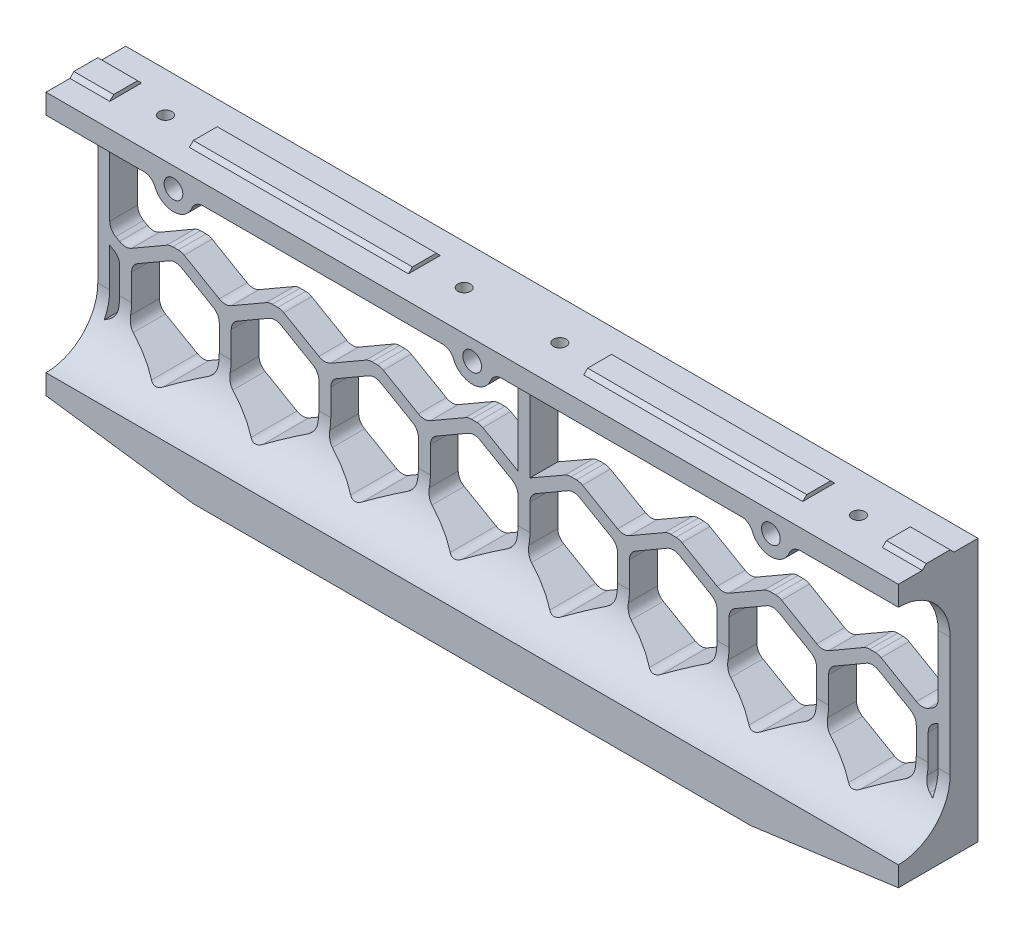
SolidWorks part; units mm, degrees
ref_plane "Front Plane" through (0, 0, 0) normal (0, 0, 1) x (1, 0, 0)
ref_plane "Top Plane" through (0, 0, 0) normal (0, 1, 0) x (1, 0, 0)
ref_plane "Right Plane" through (0, 0, 0) normal (1, 0, 0) x (0, 0, -1)
sketch "Sketch1" plane through (0, 0, 0) normal (1, 0, 0) x (0, 0, -1)
  line L0 (20, 0) -> (14, 0)
  line L1 (0, 0) -> (0, -66)
  line L2 (0, -66) -> (5, -66)
  line L3 (5, -66) -> (11, -62)
  line L4 (11, -62) -> (20, -62)
  line L5 (20, -62) -> (20, 0)
  line L6 (6, 0) -> (7, 1)
  line L7 (7, 1) -> (13, 1)
  line L8 (13, 1) -> (14, 0)
  line L9 (6, 0) -> (0, 0)
  dimension "D1" = 20
  dimension "D2" = 62
  dimension "D3" = 66
  dimension "D4" = 9
  dimension "D5" = 5
  dimension "D6" = 6
  dimension "D7" = 1
  dimension "D8" = 6
  dimension "D9" = 135
  dimension "D10" = 135
  dimension "D11" = 6
extrude "Boss-Extrude1" add sketch "Sketch1" along normal blind 107
sketch "Sketch8" plane through (0, -62, 0) normal (0, -1, 0) x (1, 0, 0)
  line L1 (0, -20) -> (70, -20)
  line L2 (0, -20) -> (0, 0)
  line L3 (0, 0) -> (70, 0)
  line L4 (70, -20) -> (70, 0)
  line L5 (0, -20) -> (70, 0) construction
  line L6 (0, 0) -> (70, -20) construction
  point P4 (35, -10)
  dimension "D1" = 70
extrude "Boss-Extrude2" add sketch "Sketch8" along normal blind 9
sketch "Sketch2" plane through (0, 1, 0) normal (0, 1, 0) x (1, 0, 0)
  line L0 (107, 14) -> (0, 14) construction
  line L1 (77, 14) -> (97, 14)
  line L2 (77, 14) -> (77, 6)
  line L3 (77, 6) -> (97, 6)
  line L4 (97, 14) -> (97, 6)
  line L5 (77, 14) -> (97, 6) construction
  line L6 (77, 6) -> (97, 14) construction
  line L7 (107, 6) -> (0, 6) construction
  line L8 (107, 13) -> (107, 7) construction
  line L14 (0, 14) -> (22, 14)
  line L15 (0, 14) -> (0, 6)
  line L16 (0, 6) -> (22, 6)
  line L17 (22, 14) -> (22, 6)
  line L18 (0, 14) -> (22, 6) construction
  line L19 (0, 6) -> (22, 14) construction
  point P4 (87, 10)
  point P17 (11, 10)
  dimension "D1" = 20
  dimension "D2" = 10
  dimension "D3" = 22
extrude "RailBump" cut sketch "Sketch2" against normal up to surface (1 mm away) up to face at (53.5, 0, -17)
sketch "Sketch3" plane through (0, 0, 0) normal (0, 1, 0) x (1, 0, 0)
  line L0 (107, 0) -> (0, 0) construction
  line L1 (22, 6) -> (22, 14) construction
  line L4 (97, 7) -> (97, 13) construction
  circle A0 centre (87, 10) radius 1.6
  circle A1 centre (12, 10) radius 1.6
  dimension "D2" = 10
  dimension "D3" = 3.2
  dimension "D4" = 10
  dimension "D5" = 10
  dimension "D1" = 10
extrude "RailMountHole" cut sketch "Sketch3" against normal blind 5
sketch "Sketch6" plane through (0, 0, 0) normal (0, 1, 0) x (1, 0, 0)
  circle A0 centre (87, 10) radius 3
  circle A1 centre (12, 10) radius 3
  dimension "D1" = 6
extrude "Mounting hole clearance" cut sketch "Sketch6" against normal blind 10 from offset 4 offset against normal yes
sketch "Sketch4" plane through (0, 0, -20) normal (0, 0, -1) x (-1, 0, 0)
  line L0 (0, 19.0302) -> (0, -62.788) construction
  line L41 (-61, -30.6998) -> (-50, -37.0506)
  line L42 (-50, -37.0506) -> (-39, -30.6998)
  line L47 (-36, -30.6998) -> (-25, -37.0506)
  line L48 (-25, -37.0506) -> (-14, -30.6998)
  line L53 (-11, -30.6998) -> (-1.5, -36.1271)
  line L55 (-107, -62) -> (-107, 0) construction
  line L56 (-104, -5) -> (-1.5, -5)
  line L57 (4.3823, -24.3489) -> (-107, -24.3489) construction
  line L61 (-39, -30.6998) -> (-36, -30.6998)
  line L62 (-107, 0) -> (0, 0) construction
  line L64 (-37.5, -58.7013) -> (-26.5, -52.3504)
  line L65 (-26.5, -52.3504) -> (-26.5, -39.6487)
  line L66 (-26.5, -39.6487) -> (-37.5, -33.2979)
  line L67 (-37.5, -33.2979) -> (-48.5, -39.6487)
  line L68 (-48.5, -39.6487) -> (-48.5, -52.3504)
  line L69 (-48.5, -52.3504) -> (-37.5, -58.7013)
  line L70 (-12.5, -58.7013) -> (-1.5, -52.3504)
  line L71 (-1.5, -52.3504) -> (-1.5, -39.6487)
  line L72 (-1.5, -39.6487) -> (-12.5, -33.2979)
  line L73 (-12.5, -33.2979) -> (-23.5, -39.6487)
  line L74 (-23.5, -39.6487) -> (-23.5, -52.3504)
  line L75 (-23.5, -52.3504) -> (-12.5, -58.7013)
  line L107 (-14, -30.6998) -> (-11, -30.6998)
  line L108 (-64, -30.6998) -> (-61, -30.6998)
  line L110 (-89, -30.7162) -> (-86, -30.6998)
  line L111 (-1.5, -5) -> (-1.5, -36.1271)
  line L118 (-86, -30.6998) -> (-75, -37.0506)
  line L119 (-75, -37.0506) -> (-64, -30.6998)
  line L124 (-104, -34.7904) -> (-100.0284, -37.0834)
  line L125 (-100.0284, -37.0834) -> (-89, -30.7162)
  line L126 (-61, -17.6718) -> (-61, -24.0227) [skipped]
  line L127 (-104, -5) -> (-104, -34.7904)
  line L131 (-76.5, -52.3504) -> (-76.5, -39.6487)
  line L132 (-76.5, -39.6487) -> (-87.5, -33.2979)
  line L133 (-87.5, -33.2979) -> (-98.5, -39.6487)
  line L134 (-98.5, -39.6487) -> (-98.5, -52.3504)
  line L135 (-98.5, -52.3504) -> (-87.5, -58.7013)
  line L136 (-87.5, -58.7013) -> (-76.5, -52.3504)
  line L137 (-51.5, -52.3504) -> (-51.5, -39.6487)
  line L138 (-51.5, -39.6487) -> (-62.5, -33.2979)
  line L139 (-62.5, -33.2979) -> (-73.5, -39.6487)
  line L140 (-73.5, -39.6487) -> (-73.5, -52.3504)
  line L141 (-73.5, -52.3504) -> (-62.5, -58.7013)
  line L142 (-62.5, -58.7013) -> (-51.5, -52.3504)
  line L158 (-101.5, -39.6979) -> (-104, -38.2545)
  line L162 (-104, -53.8184) -> (-101.5, -52.375)
  line L163 (-101.5, -52.375) -> (-101.5, -39.6979)
  line L174 (-111.0568, -24.3489) -> (-111.0568, -30.6998) [skipped]
  line L175 (-104, -38.2545) -> (-104, -53.8184)
  line L176 (-118.5604, -36.8705) -> (-124.0604, -40.046) [skipped]
  line L177 (-123.4999, -52.3505) -> (-117.9999, -55.5259) [skipped]
  line L178 (-123.4574, -39.6489) -> (-123.4574, -45.9997) [skipped]
  line L185 (0, -71) -> (0, 0) construction
  line L196 (-14, -30.6998) -> (-14, -17.9981) [skipped]
  line L197 (-14, -17.9981) -> (-25, -11.6472) [skipped]
  line L198 (-25, -11.6472) -> (-36, -17.9981) [skipped]
  line L199 (-36, -17.9981) -> (-36, -30.6998) [skipped]
  line L200 (-39, -30.6998) -> (-39, -17.9981) [skipped]
  line L201 (-39, -17.9981) -> (-50, -11.6472) [skipped]
  line L202 (-50, -11.6472) -> (-61, -17.9981) [skipped]
  line L203 (-89, -17.9817) -> (-100.0284, -11.6145) [skipped]
  line L204 (-100.0284, -11.6145) -> (-104, -13.9075) [skipped]
  line L205 (-75, -11.6472) -> (-86, -17.9981) [skipped]
  line L206 (-86, -17.9981) -> (-86, -30.6998) [skipped]
  line L207 (-89, -30.7162) -> (-89, -17.9817) [skipped]
  line L208 (-64, -17.9981) -> (-75, -11.6472) [skipped]
  line L209 (-64, -30.6998) -> (-64, -17.9981) [skipped]
  circle A4 centre (-87.5, -45.9996) radius 11 construction
  circle A5 centre (-62.5, -45.9996) radius 11 construction
  circle A9 centre (-37.5, -45.9996) radius 11 construction
  circle A10 centre (-12.5, -45.9996) radius 11 construction
  circle A14 centre (-112.4787, -46.0364) radius 10.9787 construction
  point P0 (-1.5, -36.1271)
  dimension "D5" = 3
  dimension "D7" = 3
  dimension "D8" = 22
  dimension "D9" = 5
  dimension "D15" = 22
  dimension "D17" = 3
  dimension "D18" = 3
  dimension "D19" = 12.7017
  dimension "D20" = 22
  dimension "D21" = 3
  dimension "D28" = 3
  dimension "D29" = 3
  dimension "D30" = 22
  dimension "D37" = 3
  dimension "D40" = 3
  dimension "D41" = 120
  dimension "D44" = 12.6771
  dimension "D48" = 3
  dimension "D49" = 3
extrude "HoneyPatternCutouts" cut sketch "Sketch4" against normal through all
sketch "Sketch5" plane through (107, 0, 0) normal (1, 0, 0) x (0, 0, -1)
  line L0 (0, 0) -> (0, -66) construction
  line L1 (0, -66) -> (5, -66) construction
  line L2 (6, 0) -> (0, 0) construction
  line L3 (13, -18) -> (13, -48)
  line L4 (0, -5) -> (0, -61)
  arc A0 (0, -61) -> (13, -48) centre (0, -48) ccw
  arc A1 (13, -18) -> (0, -5) centre (0, -18) ccw
  dimension "D1" = 26
  dimension "D3" = 26
  dimension "D7" = 13
  dimension "D8" = 13
  dimension "D2" = 18
  dimension "D4" = 18
  dimension "D5" = 30
  dimension "D6" = 5
extrude "Front CarveOut" cut sketch "Sketch5" against normal through all
fillet "Fillet3" radius 3 40 edges at (104, -5, -10) (104, -34.7904, -16.5) (101.5, -52.375, -16.1209) (101.5, -39.6979, -16.5) (98.5, -39.6487, -16.5) (98.5, -52.3504, -16.1252) (100.0284, -37.0834, -16.5) (89, -30.7162, -16.5) (86, -30.6998, -16.5) (87.5, -33.2979, -16.5) (76.5, -39.6487, -16.5) (87.5, -58.7013, -13.6906) (76.5, -52.3504, -16.1252) (62.5, -58.7013, -13.6906) (73.5, -52.3504, -16.1252) (73.5, -39.6487, -16.5) (62.5, -33.2979, -16.5) (75, -37.0506, -16.5) (61, -30.6998, -16.5) (64, -30.6998, -16.5) (51.5, -39.6487, -16.5) (51.5, -52.3504, -16.1252) (48.5, -39.6487, -16.5) (37.5, -33.2979, -16.5) (26.5, -39.6487, -16.5) (26.5, -52.3504, -16.1252) (37.5, -58.7013, -13.6906) (48.5, -52.3504, -16.1252) (50, -37.0506, -16.5) (39, -30.6998, -16.5) (36, -30.6998, -16.5) (25, -37.0506, -16.5) (14, -30.6998, -16.5) (11, -30.6998, -16.5) (1.5, -52.3504, -16.1252) (12.5, -58.7013, -13.6906) (23.5, -52.3504, -16.1252) (23.5, -39.6487, -16.5) (12.5, -33.2979, -16.5) (1.5, -39.6487, -16.5)
mirror "Mirror1" about plane through (0, 0, 0) normal (1, 0, 0) of "Fillet3", "Boss-Extrude2", "Front CarveOut", "RailMountHole", "RailBump", "Boss-Extrude1", "HoneyPatternCutouts", "Mounting hole clearance"
sketch "Sketch22" plane through (0, 0, 0) normal (0, 0, -1) x (-1, 0, 0)
  line L0 (1.5, -5) -> (101, -5) construction
  line L1 (80, -5) -> (70, -5)
  line L3 (-1.5, -5) -> (-101, -5) construction
  line L4 (5, -5) -> (-5, -5)
  line L6 (-80, -5) -> (-70, -5)
  arc A2 (-80, -5) -> (-70, -5) centre (-75, -5) ccw
  arc A3 (-5, -5) -> (5, -5) centre (0, -5) ccw
  arc A4 (70, -5) -> (80, -5) centre (75, -5) ccw
  dimension "D1" = 10
  dimension "D3" = 75
  dimension "D2" = 75
extrude "Boss-Extrude14" add sketch "Sketch22" along normal up to surface (20 mm away) up to face at (-87.5, -45.9996, -20)
sketch "Sketch23" plane through (0, 0, 0) normal (0, 0, -1) x (-1, 0, 0)
  line L2 (0, 0) -> (0, -5) construction
  line L3 (0, -5) -> (-5, -5) construction
  line L4 (-5, -5) -> (-75, -5) construction
  circle A0 centre (-75, -5) radius 2.35
  circle A1 centre (0, -5) radius 2.35
  circle A2 centre (75, -5) radius 2.35
  point P3 (0, 0)
  point P5 (-74.7595, -5)
  dimension "D1" = 4.7
  dimension "D2" = 75
  dimension "D3" = 75
extrude "Cut-Extrude6" cut sketch "Sketch23" along normal blind 7
fillet "Fillet4" radius 3 6 edges at (70, -5, -10) (80, -5, -10) (5, -5, -10) (-5, -5, -10) (-80, -5, -10) (-70, -5, -10)
sketch "Sketch10" plane through (0, 0, -20) normal (0, 0, -1) x (-1, 0, 0)
  line L0 (107, -62) -> (70, -62) construction
  line L2 (70, -71) -> (70, -62)
  line L3 (70, -62) -> (107, -62)
  line L5 (107, -66) -> (107, -62) construction
  line L6 (107, -62) -> (107, -66)
  line L7 (-107, -62) -> (-70, -62) construction
  line L8 (-70, -71) -> (-107, -66)
  line L9 (-70, -71) -> (-70, -62)
  line L10 (-70, -62) -> (-107, -62)
  line L12 (-107, -62) -> (-107, -66)
  line L14 (107, -66) -> (70, -71)
extrude "BasePiece" add sketch "Sketch10" against normal up to surface (20 mm away) up to face at (0, -66, 0)
